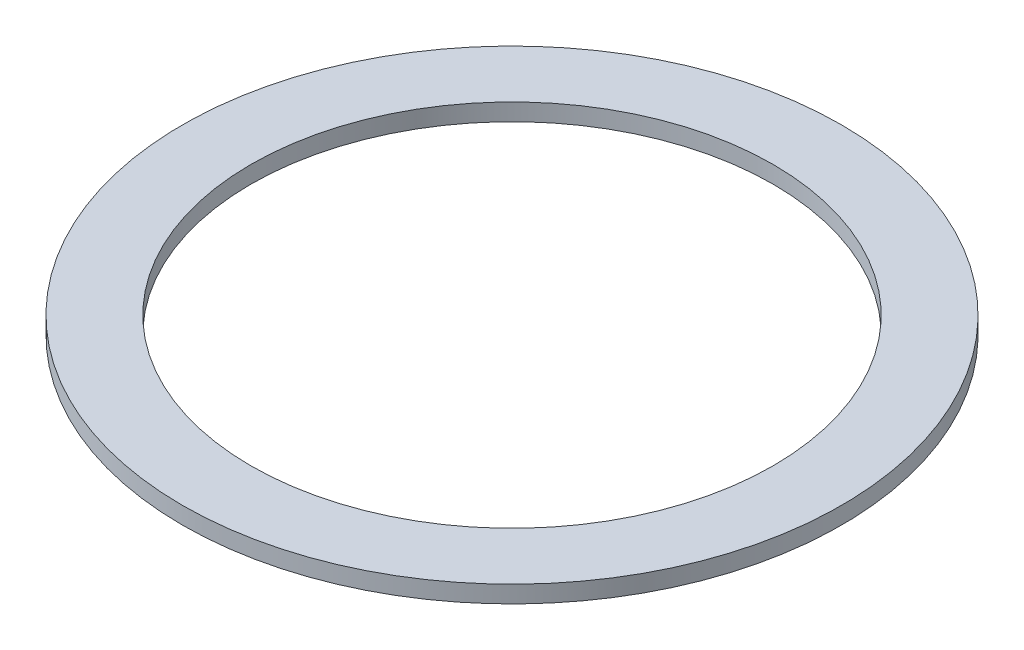
SolidWorks part; units mm, degrees
ref_plane "Front Plane" through (0, 0, 0) normal (0, 0, 1) x (1, 0, 0)
ref_plane "Top Plane" through (0, 0, 0) normal (0, 1, 0) x (1, 0, 0)
ref_plane "Right Plane" through (0, 0, 0) normal (1, 0, 0) x (0, 0, -1)
sketch "Sketch1" plane through (0, 0, 0) normal (0, 1, 0) x (1, 0, 0)
  circle A0 centre (0, 0) radius 15.25
  circle A1 centre (0, 0) radius 19.25
  dimension "D1" = 30.5
  dimension "D2" = 38.5
extrude "Boss-Extrude1" add sketch "Sketch1" along normal blind 1
